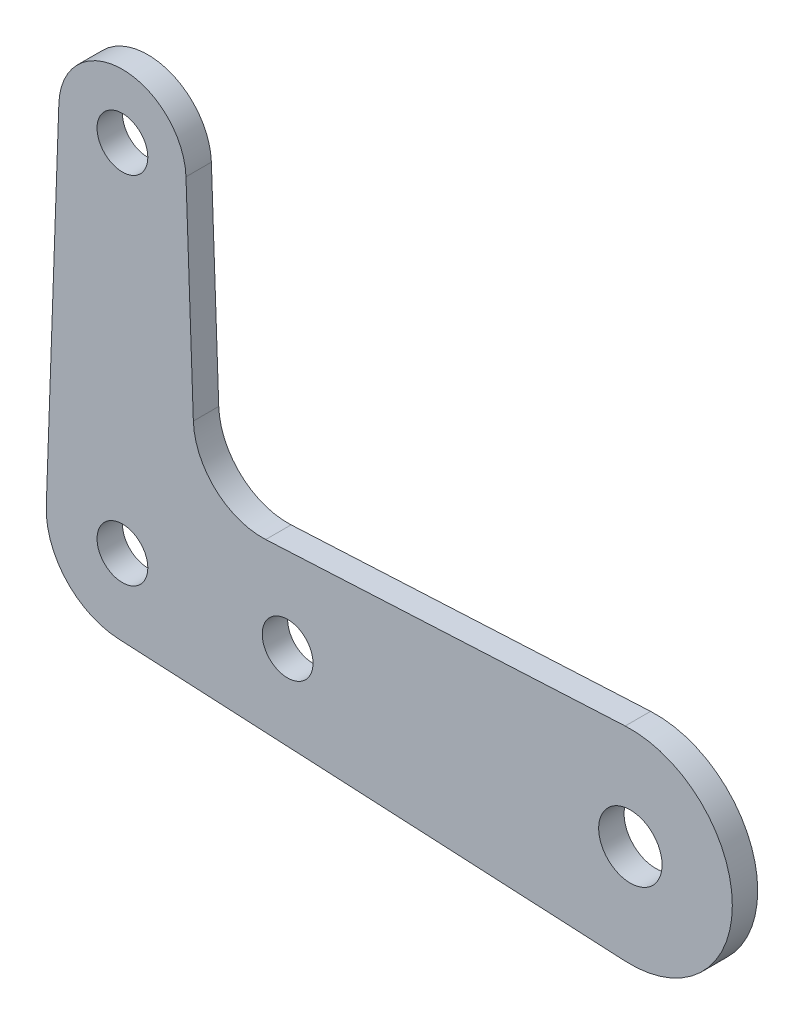
SolidWorks part; units mm, degrees
material "1023 Carbon Steel Sheet (SS)"
ref_plane "Front Plane" through (0, 0, 0) normal (0, 0, 1) x (1, 0, 0)
ref_plane "Top Plane" through (0, 0, 0) normal (0, 1, 0) x (1, 0, 0)
ref_plane "Right Plane" through (0, 0, 0) normal (1, 0, 0) x (0, 0, -1)
sketch "Sketch2" plane through (0, 0, 0) normal (0, 0, 1) x (1, 0, 0)
  line L0 (0, 17.5) -> (0, 0) construction
  line L1 (0, 0) -> (25, 0) construction
  line L2 (-3.7476, 0.1329) -> (-3.128, 17.6109)
  line L3 (3.4907, 7.3798) -> (3.128, 17.6109)
  line L4 (-0.1902, -3.7452) -> (24.7455, -5.0115)
  line L5 (7.052, 4.113) -> (24.7455, 5.0115)
  arc A0 (-3.128, 17.6109) -> (3.128, 17.6109) centre (0, 17.5) cw
  arc A1 (24.7455, 5.0115) -> (24.7455, -5.0115) centre (25, 0) cw
  arc A2 (7.052, 4.113) -> (3.4907, 7.3798) centre (6.88, 7.5) cw
  arc A3 (-0.1902, -3.7452) -> (-3.7476, 0.1329) centre (0, 0) cw
  circle A4 centre (0, 17.5) radius 1.25
  circle A5 centre (0, 0) radius 1.25
  circle A6 centre (8.13, 0) radius 1.25
  circle A7 centre (25, 0) radius 1.56
  dimension "D3" = 7.5
  dimension "D4" = 6.88
  dimension "D5" = 3.13
  dimension "D6" = 3.75
  dimension "D7" = 2.5
  dimension "D9" = 3.12
  dimension "D1" = 25
  dimension "D2" = 17.5
  dimension "D8" = 8.13
extrude "Boss-Extrude1" add sketch "Sketch2" along normal blind 1.25
